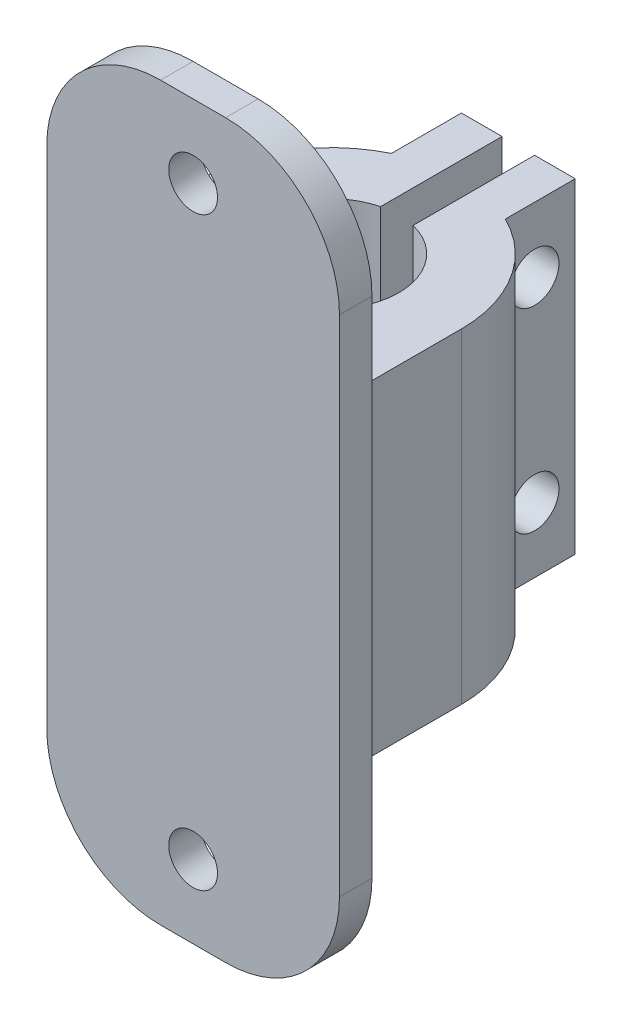
SolidWorks part; units mm, degrees
ref_plane "Front Plane" through (0, 0, 0) normal (0, 0, 1) x (1, 0, 0)
ref_plane "Top Plane" through (0, 0, 0) normal (0, 1, 0) x (1, 0, 0)
ref_plane "Right Plane" through (0, 0, 0) normal (1, 0, 0) x (0, 0, -1)
sketch "Sketch1" plane through (0, 0, 0) normal (0, 1, 0) x (1, 0, 0)
  line L0 (-28.1392, 0) -> (24.5506, 0) construction
  line L1 (0, 16.6044) -> (0, -14.6108) construction
  line L2 (-9, 0) -> (-9, 18)
  line L3 (-9, 18) -> (9, 18)
  line L4 (-9, 0) -> (9, 0)
  line L5 (9, 0) -> (9, 18)
  point P10 (0, 0)
  point P11 (0, 18)
  dimension "D1" = 9
  dimension "D2" = 18
extrude "Boss-Extrude1" add sketch "Sketch1" along normal blind 20
sketch "Sketch2" plane through (0, 20, 0) normal (0, 1, 0) x (1, 0, 0)
  line L0 (-9, 0) -> (9, 0) construction
  line L1 (9, 0) -> (9, 18) construction
  line L2 (0, 18.6431) -> (0, -3.9642) construction
  line L3 (1, 10.5277) -> (1, 18)
  line L4 (9, 18) -> (-9, 18) construction
  line L5 (1, 18) -> (0, 18)
  line L6 (-1, 10.5277) -> (-1, 18)
  line L7 (-1, 18) -> (0, 18)
  circle A0 centre (0, 6.5) radius 4.15
  arc A1 (1, 10.5277) -> (-1, 10.5277) centre (0, 6.5) cw
  line M7 (9, 18) -> (-9, 18)
  dimension "D1" = 8.3
  dimension "D2" = 6.5
  dimension "D3" = 9
  dimension "D4" = 9
  dimension "D5" = 1
  dimension "D6" = 1
extrude "Cut-Extrude1" cut sketch "Sketch2" against normal through all contours A0 L2 A1 | L2 A0 | L2 A0 L3 M7 | L2 L6 A0 M7
sketch "Sketch3" plane through (9, 0, 0) normal (1, 0, 0) x (0, 0, -1)
  line L0 (18, 20) -> (18, 0) construction
  line L1 (0, 20) -> (18, 20) construction
  line L2 (0, 0) -> (18, 0) construction
  circle A0 centre (15.5, 16) radius 1.5
  circle A1 centre (15.5, 4) radius 1.5
  dimension "D1" = 3
  dimension "D2" = 3
  dimension "D3" = 2.5
  dimension "D4" = 2.5
  dimension "D5" = 4
  dimension "D6" = 4
extrude "Cut-Extrude2" cut sketch "Sketch3" against normal through all
sketch "Sketch4" plane through (0, 0, 0) normal (0, 0, 1) x (1, 0, 0)
  line L0 (-16.8576, 10) -> (16.4765, 10) construction
  line L1 (-9, 20) -> (9, 20) construction
  line L2 (0, 26.795) -> (0, -4.8499) construction
  line L4 (-9, 32.5) -> (9, 32.5)
  line L5 (-9, 32.5) -> (-9, -12.5)
  line L6 (-9, -12.5) -> (9, -12.5)
  line L7 (9, 32.5) -> (9, -12.5)
  line L8 (-9, 32.5) -> (9, -12.5) construction
  line L9 (-9, -12.5) -> (9, 32.5) construction
  point P7 (0, 10)
  dimension "D1" = 10
  dimension "D2" = 45
  dimension "D3" = 18
extrude "Boss-Extrude2" add sketch "Sketch4" along normal blind 2
sketch "Sketch5" plane through (0, 0, 2) normal (0, 0, 1) x (1, 0, 0)
  line L0 (9, 32.5) -> (-9, 32.5) construction
  line L3 (-9, 32.5) -> (-9, -12.5) construction
  circle A0 centre (0, 28) radius 1.5
  circle A1 centre (0, -8) radius 1.5
  dimension "D1" = 3
  dimension "D2" = 36
  dimension "D3" = 4.5
  dimension "D4" = 9
extrude "Cut-Extrude3" cut sketch "Sketch5" against normal through all
fillet "Fillet1" radius 7 4 edges at (-9, -12.5, 1) (9, -12.5, 1) (-9, 32.5, 1) (9, 32.5, 1)
sketch "Sketch6" plane through (0, 0, 0) normal (0, -1, 0) x (1, 0, 0)
  line L6 (-1, -10.5277) -> (-1, -18) construction
  line L7 (-3.5, -13.6937) -> (-3.5, -18)
  line L8 (-1, -18) -> (-9, -18) construction
  line L9 (-3.5, -18) -> (-9, -18)
  line L10 (-9, -18) -> (-9, 0)
  line L11 (-9, 0) -> (-8, 0)
  line L12 (-9, 0) -> (9, 0) construction
  line L13 (-8, 0) -> (-8, -6.5)
  line L14 (0, -21.3364) -> (0, 2.7634) construction
  line L15 (8, 0) -> (8, -6.5)
  line L16 (9, 0) -> (8, 0)
  line L17 (9, -18) -> (9, 0)
  line L18 (3.5, -18) -> (9, -18)
  line L19 (3.5, -13.6937) -> (3.5, -18)
  arc A3 (-3.5, -13.6937) -> (-8, -6.5) centre (0, -6.5) cw
  arc A4 (1, -10.5277) -> (-1, -10.5277) centre (0, -6.5) ccw construction
  arc A5 (3.5, -13.6937) -> (8, -6.5) centre (0, -6.5) ccw
  dimension "D1" = 8
  dimension "D2" = 2.5
extrude "Cut-Extrude4" cut sketch "Sketch6" against normal through all
